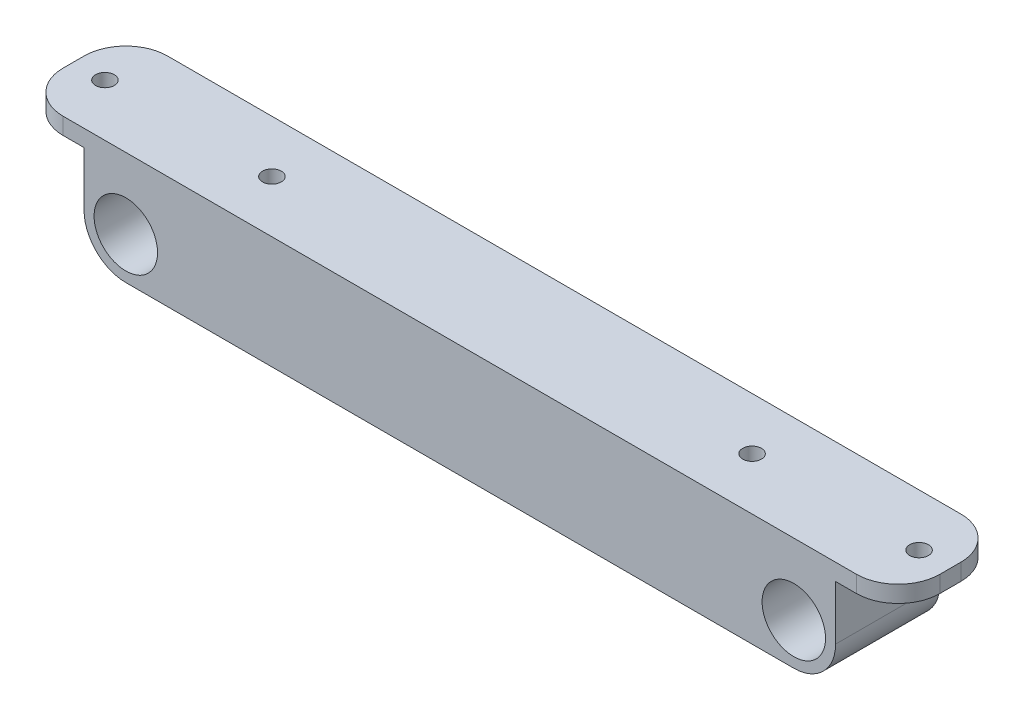
SolidWorks part; units mm, degrees
ref_plane "Front Plane" through (0, 0, 0) normal (0, 0, 1) x (1, 0, 0)
ref_plane "Top Plane" through (0, 0, 0) normal (0, 1, 0) x (1, 0, 0)
ref_plane "Right Plane" through (0, 0, 0) normal (1, 0, 0) x (0, 0, -1)
sketch "Sketch1" plane through (0, 0, 0) normal (0, 0, 1) x (1, 0, 0)
  line L0 (-80, 0) -> (0, 0) construction
  line L1 (0, 0) -> (80, 0) construction
  line L2 (-90, 0) -> (-90, 17)
  line L3 (-90, 17) -> (90, 17)
  line L4 (90, 17) -> (90, 0)
  line L5 (-70, 0) -> (-70, 13)
  line L6 (-70, 13) -> (70, 13)
  line L7 (70, 13) -> (70, 0)
  circle A0 centre (-80, 0) radius 7.6
  circle A1 centre (80, 0) radius 7.6
  arc A2 (-90, 0) -> (-70, 0) centre (-80, 0) ccw
  arc A3 (70, 0) -> (90, 0) centre (80, 0) ccw
  dimension "D2" = 15.2
  dimension "D3" = 20
  dimension "D1" = 80
  dimension "D4" = 17
  dimension "D5" = 4
extrude "Boss-Extrude1" add sketch "Sketch1" along normal blind 25
sketch "Sketch2" plane through (0, 0, 0) normal (0, 0, -1) x (-1, 0, 0)
  line L0 (-90, 17) -> (90, 17) construction
  line L1 (-16, 17) -> (-46, 17)
  line L2 (-16, 17) -> (-16, -10)
  line L3 (-16, -10) -> (-46, -10)
  line L4 (-46, 17) -> (-46, -10)
  line L5 (70, 13) -> (-70, 13) construction
  point P8 (-31, -10)
  point P9 (0, 13)
  dimension "D1" = 23
  dimension "D2" = 31
  dimension "D3" = 30
extrude "Boss-Extrude2" add sketch "Sketch2" against normal up to surface (25 mm away) up to face at (-72.4, 0, 25)
sketch "Sketch3" plane through (0, 0, 0) normal (0, 0, -1) x (-1, 0, 0)
  line L0 (80, -10) -> (-12, -10)
  line L1 (-42, -10) -> (-80, -10)
  line L2 (-12, -10) -> (-42, -10)
  line L10 (90, 0) -> (90, 17)
  line L11 (90, 17) -> (-90, 17)
  line L12 (-90, 17) -> (-90, 0)
  line L13 (-70, 0) -> (-70, 13)
  line L14 (-70, 13) -> (-46, 13)
  line L15 (-46, 13) -> (-46, -10)
  line L16 (-46, -10) -> (-16, -10)
  line L17 (-16, -10) -> (-16, 13)
  line L18 (-16, 13) -> (70, 13)
  line L19 (70, 13) -> (70, 0)
  line L20 (90, 0) -> (90, 17)
  line L21 (90, 17) -> (-90, 17)
  line L22 (-90, 17) -> (-90, 0)
  circle A0 centre (80, 0) radius 7.6
  circle A1 centre (-80, 0) radius 7.6
  arc A2 (-90, 0) -> (-70, 0) centre (-80, 0) ccw
  arc A3 (70, 0) -> (90, 0) centre (80, 0) ccw
  arc A4 (-90, 0) -> (-80, -10) centre (-80, 0) ccw
  arc A5 (80, -10) -> (90, 0) centre (80, 0) ccw
  dimension "D1" = 0
extrude "Boss-Extrude3" add sketch "Sketch3" against normal blind 2
ref_plane "Plane1" through (0, 0, 12.5) normal (0, 0, 1) x (1, 0, 0)
mirror "Mirror1" about plane through (0, 0, 12.5) normal (0, 0, 1) of "Boss-Extrude3"
chamfer "Chamfer1" distance 5 angle 45 2 edges at (-70, 13, 12.5) (70, 13, 12.5)
sketch "Sketch5" plane through (-90, 0, 0) normal (-1, 0, 0) x (0, 0, 1)
  line L0 (25, 17) -> (25, 0) construction
  line L1 (0, 17) -> (25, 17)
  line L2 (0, 17) -> (0, 13)
  line L3 (0, 13) -> (25, 13)
  line L4 (25, 17) -> (25, 13)
  dimension "D1" = 4
extrude "Boss-Extrude4" add sketch "Sketch5" along normal blind 15
sketch "Sketch6" plane through (0, 13, 0) normal (0, -1, 0) x (-1, 0, 0)
  line L0 (90, -25) -> (105, 0) construction
  circle A0 centre (97.5, -12.5) radius 2.25
  dimension "D1" = 4.5
extrude "Cut-Extrude2" cut sketch "Sketch6" against normal blind 15
fillet "Fillet1" radius 10 2 edges at (-105, 15, 0) (-105, 15, 25)
mirror "Mirror2" about plane through (0, 0, 0) normal (1, 0, 0) of "Fillet1", "Boss-Extrude4"
mirror "Mirror4" about plane through (0, 0, 0) normal (1, 0, 0) of "Cut-Extrude2"
sketch "Sketch7" plane through (0, 17, 0) normal (0, 1, 0) x (1, 0, 0)
  circle A0 centre (-57.5, -12.5) radius 2.25
  circle A1 centre (57.5, -12.5) radius 2.25
  circle A2 centre (-97.5, -12.5) radius 2.25 construction
  circle A3 centre (97.5, -12.5) radius 2.25 construction
  dimension "D1" = 40
  dimension "D2" = 40
extrude "Cut-Extrude3" cut sketch "Sketch7" against normal blind 15
sketch "Sketch8" plane through (0, -10, 0) normal (0, -1, 0) x (1, 0, 0)
  line L0 (20, 19) -> (20, 6)
  line L1 (16, 23) -> (46, 23)
  line L2 (16, 23) -> (16, 2)
  line L3 (16, 2) -> (46, 2)
  line L4 (46, 23) -> (46, 2)
  line L5 (20, 6) -> (42, 6)
  line L6 (42, 19) -> (42, 6)
  line L7 (20, 19) -> (42, 19)
  circle A0 centre (20, 19) radius 1.95
  circle A1 centre (42, 19) radius 1.95
  circle A2 centre (42, 6) radius 1.95
  circle A3 centre (20, 6) radius 1.95
  dimension "D2" = 3.9
  dimension "D1" = 4
extrude "Cut-Extrude4" cut sketch "Sketch8" against normal blind 15 contours L7 A0 L0 | L0 A0 L7 | L7 A1 L6 | L6 A1 L7 | L5 A2 L6 | L6 A2 L5 | L5 A3 L0 | L0 A3 L5
